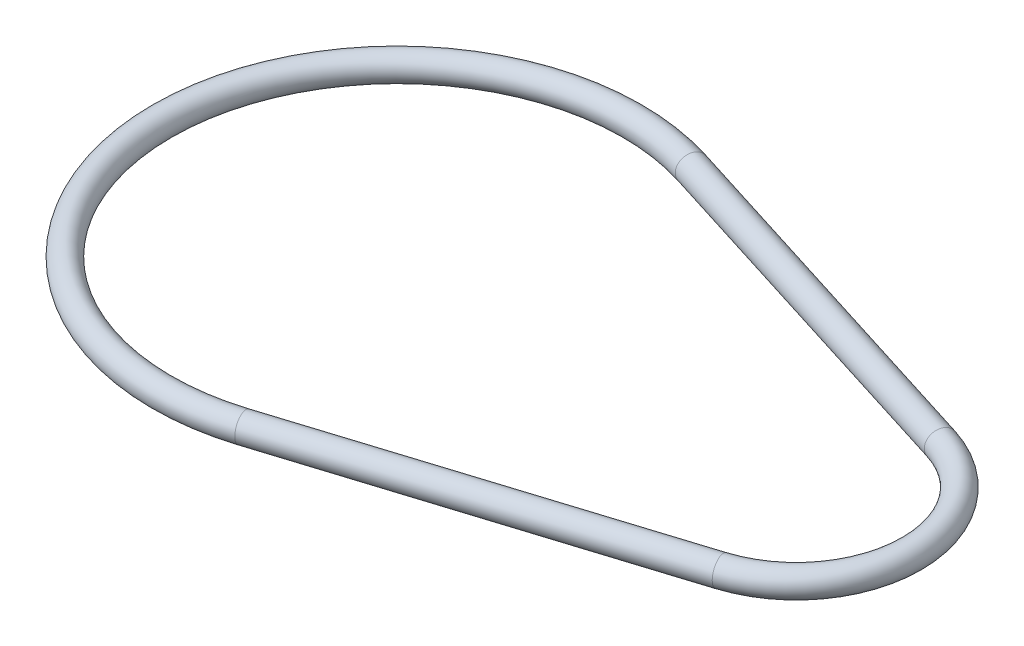
SolidWorks part; units mm, degrees
ref_plane "前视基准面" through (0, 0, 0) normal (0, 0, 1) x (1, 0, 0)
ref_plane "上视基准面" through (0, 0, 0) normal (0, 1, 0) x (1, 0, 0)
ref_plane "右视基准面" through (0, 0, 0) normal (1, 0, 0) x (0, 0, -1)
sketch "草图1" plane through (0, 0, 0) normal (0, 1, 0) x (1, 0, 0)
  line L0 (7.95, -25.2794) -> (48.9, -12.4012)
  line L1 (7.95, 25.2794) -> (48.9, 12.4012)
  arc A0 (7.95, 25.2794) -> (7.95, -25.2794) centre (0, 0) ccw
  arc A1 (48.9, -12.4012) -> (48.9, 12.4012) centre (45, 0) ccw
  dimension "D1" = 26
  dimension "D2" = 53
  dimension "D3" = 45
sweep "扫描1" add path "草图1" circular profile diameter 3 parameters "D3"=3
